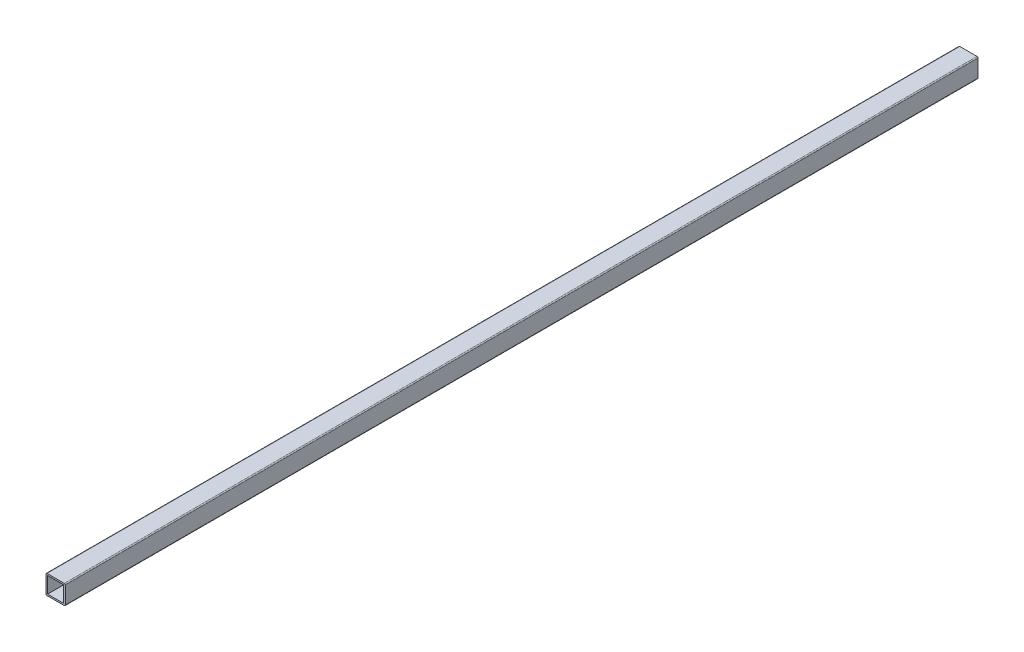
SolidWorks part; units mm, degrees
ref_plane "정면" through (0, 0, 0) normal (0, 0, 1) x (1, 0, 0)
ref_plane "윗면" through (0, 0, 0) normal (0, 1, 0) x (1, 0, 0)
ref_plane "우측면" through (0, 0, 0) normal (1, 0, 0) x (0, 0, -1)
sketch "스케치1" plane through (0, 0, 0) normal (0, 0, 1) x (1, 0, 0)
  line L1 (0, 0) -> (19, 0)
  line L2 (0, 0) -> (0, -19)
  line L3 (0, -19) -> (19, -19)
  line L4 (19, 0) -> (19, -19)
  line L5 (1.56, -1.56) -> (17.44, -1.56)
  line L6 (1.56, -1.56) -> (1.56, -17.44)
  line L7 (1.56, -17.44) -> (17.44, -17.44)
  line L8 (17.44, -1.56) -> (17.44, -17.44)
  dimension "D1" = 19
  dimension "D2" = 19
  dimension "D3" = 15.88
  dimension "D4" = 15.88
  dimension "D5" = 1.56
  dimension "D6" = 1.56
extrude "보스-돌출1" add sketch "스케치1" along normal blind 900
fillet "필렛2" radius 1 4 edges at (0, -19, 450) (0, 0, 450) (19, -19, 450) (19, 0, 450)
